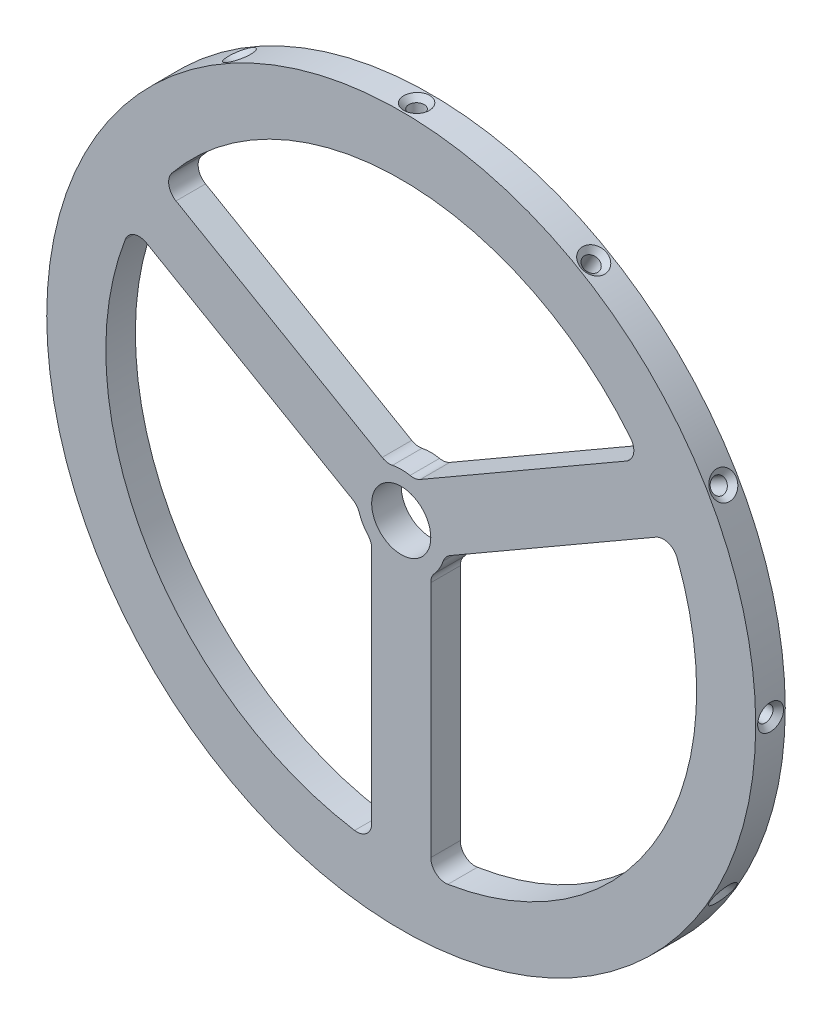
SolidWorks part; units mm, degrees
ref_plane "Front Plane" through (0, 0, 0) normal (0, 0, 1) x (1, 0, 0)
ref_plane "Top Plane" through (0, 0, 0) normal (0, 1, 0) x (1, 0, 0)
ref_plane "Right Plane" through (0, 0, 0) normal (1, 0, 0) x (0, 0, -1)
sketch "Sketch1" plane through (0, 0, 0) normal (0, 0, 1) x (1, 0, 0)
  line L0 (0, 0) -> (0, -60) construction
  line L1 (0, 0) -> (51.9615, 30) construction
  line L2 (0, 0) -> (-51.9615, 30) construction
  line L3 (-2.5, 4.3301) -> (49.4615, 34.3301) construction
  line L4 (-5, -59.7913) -> (-5, -59.7229)
  line L5 (-5, -6.6144) -> (-5, -46.9042)
  line L6 (-3.2282, 7.6373) -> (-38.1202, 27.7822)
  line L7 (5, -59.7913) -> (5, -50)
  line L8 (3.2282, 7.6373) -> (38.1202, 27.7822)
  line L9 (8.2282, -1.0229) -> (43.1202, 19.122)
  line L10 (-8.2282, -1.0229) -> (-43.1202, 19.122)
  line L11 (5, -6.6144) -> (5, -46.9042)
  line L12 (-54.2808, 25.5655) -> (-54.2215, 25.5313)
  line L13 (-49.2808, 34.2258) -> (-49.2215, 34.1916)
  line L14 (49.2808, 34.2258) -> (49.4615, 34.3301)
  line L15 (54.2808, 25.5655) -> (45.8013, 20.6699)
  circle A0 centre (0, 0) radius 60
  arc A1 (-7.1087, -2.391) -> (-5.625, -4.9608) centre (0, 0) ccw
  arc A2 (-46.7055, 17.8494) -> (-7.8947, -49.3728) centre (0, 0) ccw
  circle A3 centre (0, 0) radius 50 construction
  arc A4 (38.8107, 31.5234) -> (-38.8107, 31.5234) centre (0, 0) ccw
  arc A5 (7.8947, -49.3728) -> (46.7055, 17.8494) centre (0, 0) ccw
  circle A6 centre (0, 0) radius 5
  arc A7 (5.625, -4.9608) -> (7.1087, -2.391) centre (0, 0) ccw
  arc A8 (1.4837, 7.3518) -> (-1.4837, 7.3518) centre (0, 0) ccw
  arc A9 (38.1202, 27.7822) -> (38.8107, 31.5234) centre (36.8702, 29.9473) ccw
  arc A10 (-38.1202, 27.7822) -> (-38.8107, 31.5234) centre (-36.8702, 29.9473) cw
  arc A11 (-43.1202, 19.122) -> (-46.7055, 17.8494) centre (-44.3702, 16.9569) ccw
  arc A12 (3.2282, 7.6373) -> (1.4837, 7.3518) centre (1.9782, 9.8024) cw
  arc A13 (-3.2282, 7.6373) -> (-1.4837, 7.3518) centre (-1.9782, 9.8024) ccw
  arc A14 (-8.2282, -1.0229) -> (-7.1087, -2.391) centre (-9.4782, -3.188) cw
  arc A15 (-5, -6.6144) -> (-5.625, -4.9608) centre (-7.5, -6.6144) ccw
  arc A16 (5, -6.6144) -> (5.625, -4.9608) centre (7.5, -6.6144) cw
  arc A17 (8.2282, -1.0229) -> (7.1087, -2.391) centre (9.4782, -3.188) ccw
  arc A18 (43.1202, 19.122) -> (46.7055, 17.8494) centre (44.3702, 16.9569) cw
  arc A19 (-5, -46.9042) -> (-7.8947, -49.3728) centre (-7.5, -46.9042) cw
  arc A20 (5, -46.9042) -> (7.8947, -49.3728) centre (7.5, -46.9042) ccw
  point P36 (40.5842, 29.2048)
  point P43 (2.3412, 7.1252)
  point P52 (5, -5.5902)
  point P55 (7.3412, -1.535)
  point P62 (5, -49.7494)
  dimension "D1" = 120
  dimension "D2" = 10
  dimension "15" = 15
  dimension "D5" = 10
  dimension "D7" = 2.5
  dimension "D3" = 120
  dimension "D4" = 120
  dimension "D8" = 0
  dimension "D6" = 5
extrude "Boss-Extrude1" add sketch "Sketch1" along normal blind 5 contours A0 A20 L11 A16 A7 A17 L9 A18 A5 A13 L6 A10 A4 A9 L8 A12 A8 A6 L5 A19 A2 A11 L10 A14 A1 A15
ref_plane "Plane1" through (0, -60, 0) normal (0, -1, 0) x (-1, 0, 0)
hole_wizard "CSK for M2 Flat Head Machine Screw2" positions "3DSketch11" profile "Sketch9" countersink size "M2" standard "ANSI Metric"
sketch3d "3DSketch11"
  point P0 (-0.0762, -60, 2.4775)
sketch "Sketch9" plane through (-0.0762, -60, 2.4775) normal (0, 0, 1) x (1, -0.0013, 0)
  line L0 (0, 0) -> (0, 5.7811)
  line L1 (0, 5.7811) -> (1.3, 5)
  line L2 (1.3, 5) -> (1.3, 0.9)
  line L3 (1.3, 0.9) -> (2.2, 0)
  line L5 (2.2, 0) -> (0, 0)
  line L6 (-1.3, 0.9) -> (-2.2, 0) construction
  line L10 (0, 5.7811) -> (-1.3, 5) construction
  line L11 (0, -6.35) -> (0, 107.95) construction
  dimension "Hole Dia." = 2.6
  dimension "Hole Depth" = 5
  dimension "Near C'Sink Dia." = 4.4
  dimension "Near C'Sink Angle" = 90
  dimension "Drill Angle" = 118
pattern_circular "CirPattern2" count 12 over 360 about axis through (0, 0, 5) along (0, 0, 1) of "CSK for M2 Flat Head Machine Screw2"
